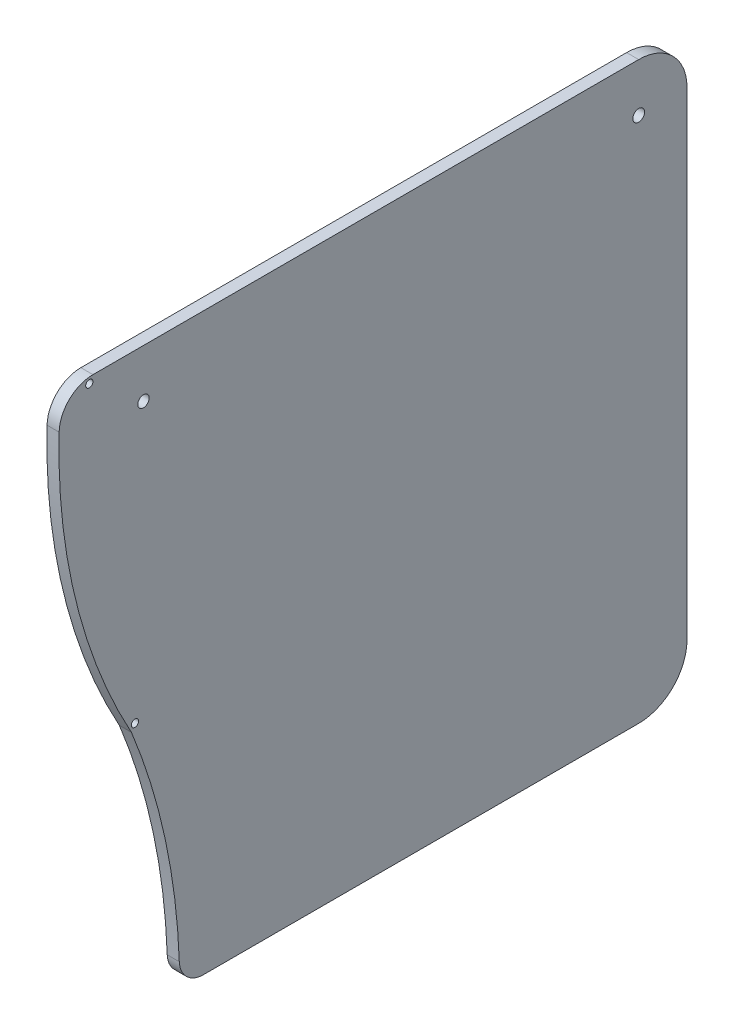
SolidWorks part; units mm, degrees
ref_plane "Front Plane" through (0, 0, 0) normal (0, 0, 1) x (1, 0, 0)
ref_plane "Top Plane" through (0, 0, 0) normal (0, 1, 0) x (1, 0, 0)
ref_plane "Right Plane" through (0, 0, 0) normal (1, 0, 0) x (0, 0, -1)
sketch "Sketch1" plane through (0, 0, 0) normal (1, 0, 0) x (0, 0, -1)
  line L1 (-82.55, 75.565) -> (82.55, 75.565)
  line L2 (-82.55, 75.565) -> (-82.55, -75.565)
  line L3 (-82.55, -75.565) -> (82.55, -75.565)
  line L4 (82.55, 75.565) -> (82.55, -75.565)
  line L9 (69.85, 75.565) -> (69.85, -75.565) construction
  circle A0 centre (69.85, 62.865) radius 1.55
  arc A1 (69.85, -75.565) -> (82.55, -62.865) centre (69.85, -62.865) ccw
  arc A2 (82.55, 62.865) -> (69.85, 75.565) centre (69.85, 62.865) ccw
  point P4 (-82.55, 0)
  point P6 (0, 75.565)
  dimension "D6" = 3.1
  dimension "D1" = 165.1
  dimension "D3" = 151.13
  dimension "D4" = 12.7
  dimension "D5" = 12.7
  dimension "D7" = 12.7
extrude "Boss-Extrude1" add sketch "Sketch1" along normal blind 3.175 contours L9 L1 L2 L3 A0 | L1 L9 A1 L4
sketch "Sketch2" plane through (3.175, 0, 0) normal (1, 0, 0) x (0, 0, -1)
  line L0 (-63.5, -75.565) -> (-50.8, -75.565)
  line L2 (-82.55, 62.865) -> (-82.55, -75.565)
  line L3 (-82.55, -75.565) -> (-63.5, -75.565)
  line L5 (-82.55, 75.565) -> (-82.0199, 75.565)
  line L6 (-82.55, 75.565) -> (69.85, 75.565) construction
  line L7 (-82.55, 75.565) -> (-82.55, 62.865)
  line L8 (-63.5, -10.9153) -> (-63.5, -75.565)
  line L9 (82.55, 62.865) -> (82.55, -62.865) construction
  line L11 (-50.8, 75.565) -> (-50.8, -75.565) construction
  line L12 (-82.55, -75.565) -> (69.85, -75.565) construction
  arc A1 (-82.0199, 75.565) -> (-63.5, -10.9153) centre (69.85, 62.865) ccw
  arc A4 (-50.8, -75.565) -> (-63.5, -10.9153) centre (-221.7004, -75.565) ccw
  line M6 (69.85, 75.565) -> (-82.55, 75.565)
  line M7 (-82.55, 75.565) -> (-82.55, -75.565)
  line M8 (-82.55, -75.565) -> (69.85, -75.565)
  dimension "D1" = 146.05
  dimension "D2" = 133.35
extrude "Cut-Extrude1" cut sketch "Sketch2" against normal through all contours A1 M7 M8 | A1 M6 M7 | A4 L8 M8
fillet "Fillet1" radius 8.89 1 edges at (1.5875, 75.565, 82.0199)
sketch "Sketch3" plane through (3.175, 0, 0) normal (1, 0, 0) x (0, 0, -1)
  line L0 (-73.6094, 75.565) -> (69.85, 75.565) construction
  circle A0 centre (-60.325, 62.865) radius 1.5
  dimension "D1" = 3
  dimension "D2" = 9.525
  dimension "D3" = 12.7
extrude "Cut-Extrude2" cut sketch "Sketch3" against normal through all
sketch "Sketch4" plane through (3.175, 0, 0) normal (1, 0, 0) x (0, 0, -1)
  line L0 (-73.6094, 72.39) -> (-73.6094, 75.565)
  line L1 (-60.7219, -9.3782) -> (-63.5, -10.9153)
  line L2 (-74.5619, 73.9775) -> (-73.6094, 73.9775) construction
  line L3 (-62.1109, -10.1468) -> (-62.5721, -9.3134) construction
  arc A0 (-82.4963, 66.911) -> (-63.5, -10.9153) centre (69.85, 62.865) ccw construction
  arc A1 (-73.6094, 75.565) -> (-82.4963, 66.911) centre (-73.6094, 66.675) ccw construction
  arc A2 (-82.4963, 66.911) -> (-63.5, -10.9153) centre (69.85, 62.865) ccw
  arc A3 (-73.6094, 75.565) -> (-82.4963, 66.911) centre (-73.6094, 66.675) ccw
  arc A4 (-73.6094, 72.39) -> (-79.3224, 66.8267) centre (-73.6094, 66.675) ccw
  arc A5 (-79.3224, 66.8267) -> (-60.7219, -9.3782) centre (69.85, 62.865) ccw
  circle A6 centre (-74.5619, 73.9775) radius 0.9525
  circle A7 centre (-62.5721, -9.3134) radius 0.9525
  dimension "D2" = 1.905
  dimension "D1" = 3.175
extrude "Cut-Extrude3" cut sketch "Sketch4" against normal through all contours A6 | A7
fillet "Fillet2" radius 6.35 1 edges at (1.5875, -75.565, 50.8)
equation "\"bottomThickness\"= .25in"
equation "\"wallThickness\"= .125in"
equation "\"D1@Boss-Extrude1\"=\"wallThickness\""
